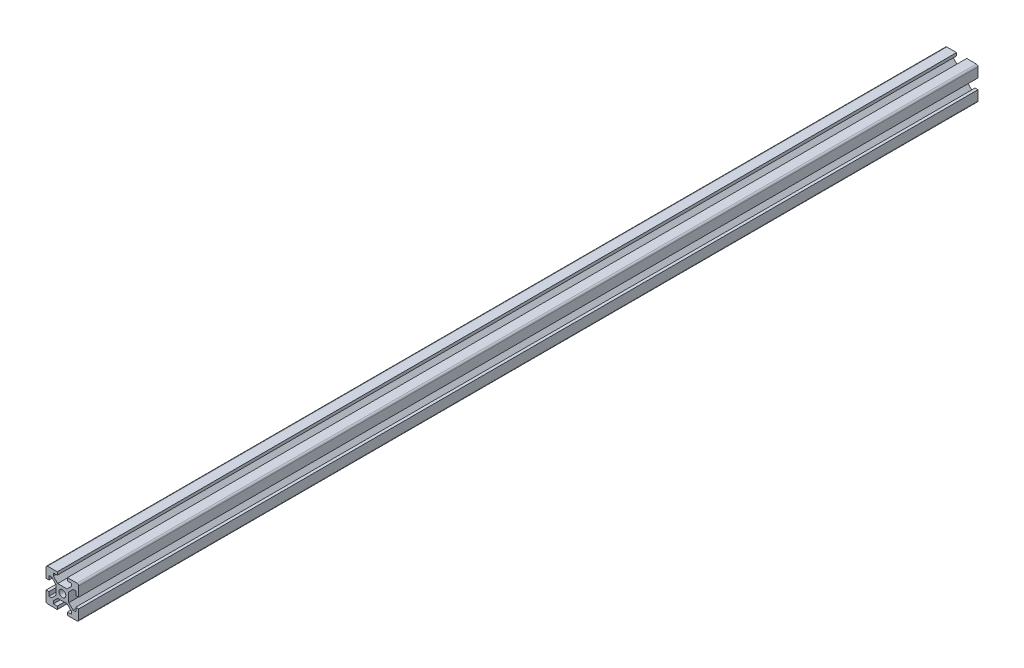
SolidWorks part; units mm, degrees
material "6063-T1"
ref_plane "Front Plane" through (0, 0, 0) normal (0, 0, 1) x (1, 0, 0)
ref_plane "Top Plane" through (0, 0, 0) normal (0, 1, 0) x (1, 0, 0)
ref_plane "Right Plane" through (0, 0, 0) normal (1, 0, 0) x (0, 0, -1)
sketch "Sketch1" plane through (0, 0, 0) normal (0, 0, 1) x (1, 0, 0)
  line L0 (-3.1, 10) -> (-3.1, 8.2007)
  line L1 (-10, 10) -> (-3.1, 10)
  line L2 (-10, 10) -> (-10, 3.1)
  line L3 (-10, -10) -> (-3.1, -10)
  line L4 (10, 10) -> (10, 3.1)
  line L5 (-10, 10) -> (10, -10) construction
  line L6 (-10, -10) -> (10, 10) construction
  line L7 (-3.1, 8.2007) -> (-5.5, 8.2007)
  line L8 (-5.5, 8.2007) -> (-5.5, 6.5607)
  line L9 (-5.5, 6.5607) -> (-2.84, 3.9007)
  line L10 (-2.84, 3.9007) -> (2.84, 3.9007)
  line L11 (2.84, 3.9007) -> (5.5, 6.5607)
  line L12 (5.5, 6.5607) -> (5.5, 8.2007)
  line L13 (5.5, 8.2007) -> (3.1, 8.2007)
  line L14 (3.1, 8.2007) -> (3.1, 10)
  line L15 (-3.1, 8.2007) -> (3.1, 8.2007) construction
  line L16 (-5.5, 6.5607) -> (5.5, 6.5607) construction
  line L17 (3.1, 10) -> (10, 10)
  line L18 (8.2007, 3.1) -> (8.2007, 5.5)
  line L19 (8.2007, 5.5) -> (6.5607, 5.5)
  line L20 (6.5607, 5.5) -> (3.9007, 2.84)
  line L21 (3.9007, 2.84) -> (3.9007, -2.84)
  line L22 (3.9007, -2.84) -> (6.5607, -5.5)
  line L23 (6.5607, -5.5) -> (8.2007, -5.5)
  line L24 (8.2007, -5.5) -> (8.2007, -3.1)
  line L25 (8.2007, 3.1) -> (8.2007, -3.1) construction
  line L26 (6.5607, 5.5) -> (6.5607, -5.5) construction
  line L27 (10, 3.1) -> (8.2007, 3.1)
  line L28 (8.2007, -3.1) -> (10, -3.1)
  line L29 (3.1, -8.2007) -> (5.5, -8.2007)
  line L30 (5.5, -8.2007) -> (5.5, -6.5607)
  line L31 (5.5, -6.5607) -> (2.84, -3.9007)
  line L32 (2.84, -3.9007) -> (-2.84, -3.9007)
  line L33 (-2.84, -3.9007) -> (-5.5, -6.5607)
  line L34 (-5.5, -6.5607) -> (-5.5, -8.2007)
  line L35 (-5.5, -8.2007) -> (-3.1, -8.2007)
  line L36 (3.1, -8.2007) -> (-3.1, -8.2007) construction
  line L37 (5.5, -6.5607) -> (-5.5, -6.5607) construction
  line L38 (3.1, -10) -> (3.1, -8.2007)
  line L39 (-3.1, -8.2007) -> (-3.1, -10)
  line L40 (-8.2007, -3.1) -> (-8.2007, -5.5)
  line L41 (-8.2007, -5.5) -> (-6.5607, -5.5)
  line L42 (-6.5607, -5.5) -> (-3.9007, -2.84)
  line L43 (-3.9007, -2.84) -> (-3.9007, 2.84)
  line L44 (-3.9007, 2.84) -> (-6.5607, 5.5)
  line L45 (-6.5607, 5.5) -> (-8.2007, 5.5)
  line L46 (-8.2007, 5.5) -> (-8.2007, 3.1)
  line L47 (-8.2007, -3.1) -> (-8.2007, 3.1) construction
  line L48 (-6.5607, -5.5) -> (-6.5607, 5.5) construction
  line L49 (-10, -3.1) -> (-8.2007, -3.1)
  line L50 (-8.2007, 3.1) -> (-10, 3.1)
  line L51 (10, -3.1) -> (10, -10)
  line L52 (3.1, -10) -> (10, -10)
  line L53 (-10, -3.1) -> (-10, -10)
  point P0 (0, 0)
  point P8 (0, 8.2007)
  point P18 (0, 3.9007)
  dimension "D1" = 20
  dimension "D2" = 20
  dimension "D3" = 5.68
  dimension "D4" = 6.2
  dimension "D5" = 4.3
  dimension "D6" = 11
  dimension "D7" = 0.75
  dimension "D8" = 4
extrude "Boss-Extrude1" add sketch "Sketch1" along normal mid plane 550
sketch "Sketch2" plane through (0, 0, 275) normal (0, 0, 1) x (1, 0, 0)
  circle A0 centre (0, 0) radius 2.1
  dimension "D1" = 4.2
extrude "Cut-Extrude1" cut sketch "Sketch2" against normal through all
fillet "Fillet1" radius 1 4 edges at (-10, -10, 0) (-10, 10, 0) (10, -10, 0) (10, 10, 0)
